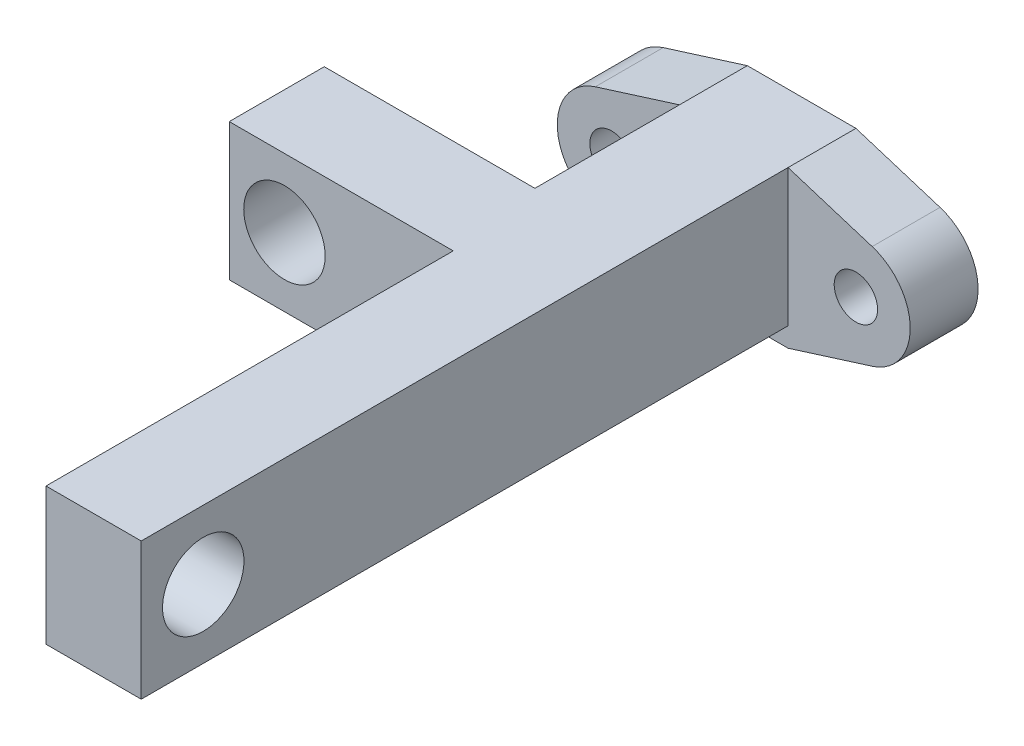
SolidWorks part; units mm, degrees
ref_plane "Front Plane" through (0, 0, 0) normal (0, 0, 1) x (1, 0, 0)
ref_plane "Top Plane" through (0, 0, 0) normal (0, 1, 0) x (1, 0, 0)
ref_plane "Right Plane" through (0, 0, 0) normal (1, 0, 0) x (0, 0, -1)
sketch "Esboço1" plane through (0, 0, 0) normal (0, 0, 1) x (1, 0, 0)
  line L12 (-10.1991, -3.8177) -> (-4, -5.765)
  line L13 (-4, -5.765) -> (4, -5.765)
  line L14 (4, -5.765) -> (10.1978, -3.8173)
  line L15 (10.196, 3.8191) -> (4, 5.763)
  line L16 (4, 5.763) -> (-4, 5.763)
  line L17 (-4, 5.763) -> (-10.1991, 3.8155)
  line L18 (-10.1991, -3.8177) -> (-4, -5.765)
  line L19 (-4, -5.765) -> (4, -5.765)
  line L20 (4, -5.765) -> (10.1978, -3.8173)
  line L21 (10.196, 3.8191) -> (4, 5.763)
  line L22 (4, 5.763) -> (-4, 5.763)
  line L23 (-4, 5.763) -> (-10.1991, 3.8155)
  arc A4 (-10.1991, 3.8155) -> (-10.1991, -3.8177) centre (-9.0001, -0.0011) ccw
  arc A5 (10.1978, -3.8173) -> (10.196, 3.8191) centre (8.998, 0.0006) ccw
  arc A6 (-10.1991, 3.8155) -> (-10.1991, -3.8177) centre (-9.0001, -0.0011) ccw
  arc A7 (10.1978, -3.8173) -> (10.196, 3.8191) centre (8.998, 0.0006) ccw
  circle A8 centre (8.998, 0.0006) radius 1.5982
  circle A9 centre (8.998, 0.0006) radius 1.5982
  circle A11 centre (-9.0001, -0.0011) radius 1.601
  circle A12 centre (-9.0001, -0.0011) radius 1.601
  dimension "D1" = 0
  dimension "D2" = 0
  dimension "D3" = 0
extrude "Ressalto-extrusão1" add sketch "Esboço1" along normal blind 5
sketch "Esboço2" plane through (0, 0, 5) normal (0, 0, 1) x (1, 0, 0)
  line L1 (4, -4.3345) -> (-4, -4.3345)
  line L2 (4, -4.3345) -> (4, 5.763)
  line L3 (4, 5.763) -> (-4, 5.763)
  line L4 (-4, -4.3345) -> (-4, 5.763)
extrude "Ressalto-extrusão2" add sketch "Esboço2" along normal up to vertex (17.65 mm away)
sketch "Esboço3" plane through (-4, 0, 0) normal (-1, 0, 0) x (0, 0, 1)
  line L1 (22.65, 5.763) -> (15.65, 5.763)
  line L2 (22.65, 5.763) -> (22.65, -4.3345)
  line L3 (22.65, -4.3345) -> (15.65, -4.3345)
  line L4 (15.65, 5.763) -> (15.65, -4.3345)
  dimension "D1" = 7
extrude "Ressalto-extrusão3" add sketch "Esboço3" along normal up to vertex (15.5157 mm away)
sketch "Esboço4" plane through (0, 0, 15.65) normal (0, 0, -1) x (-1, 0, 0)
  line L0 (19.5157, 0.7142) -> (11.3817, 0.7142) construction
  line L1 (19.5157, 5.763) -> (19.5157, -4.3345) construction
  circle A0 centre (15.4487, 0.7142) radius 3
  dimension "D1" = 6
extrude "Corte-extrusão1" cut sketch "Esboço4" against normal blind 13
sketch "Esboço5" plane through (0, 0, 22.65) normal (0, 0, 1) x (1, 0, 0)
  line L0 (4, -4.3345) -> (4, 5.763) construction
  line L1 (4, -4.3345) -> (-3.0157, -4.3345)
  line L2 (4, -4.3345) -> (4, 5.763)
  line L3 (4, 5.763) -> (-3.0157, 5.763)
  line L4 (-3.0157, -4.3345) -> (-3.0157, 5.763)
  line L5 (-19.5157, -4.3345) -> (4, -4.3345) construction
  line L6 (4, 5.763) -> (-19.5157, 5.763) construction
  line L7 (-3.0157, -3.9498) -> (-3.0157, 5.9304) construction
extrude "Ressalto-extrusão4" add sketch "Esboço5" along normal blind 30
sketch "Esboço6" plane through (4, 0, 0) normal (1, 0, 0) x (0, 0, -1)
  line L0 (-52.65, 0.7142) -> (-43.5111, 0.7142) construction
  line L1 (-52.65, -4.3345) -> (-52.65, 5.763) construction
  circle A0 centre (-48.0806, 0.7142) radius 3
  dimension "D1" = 6
extrude "Corte-extrusão2" cut sketch "Esboço6" against normal blind 30
